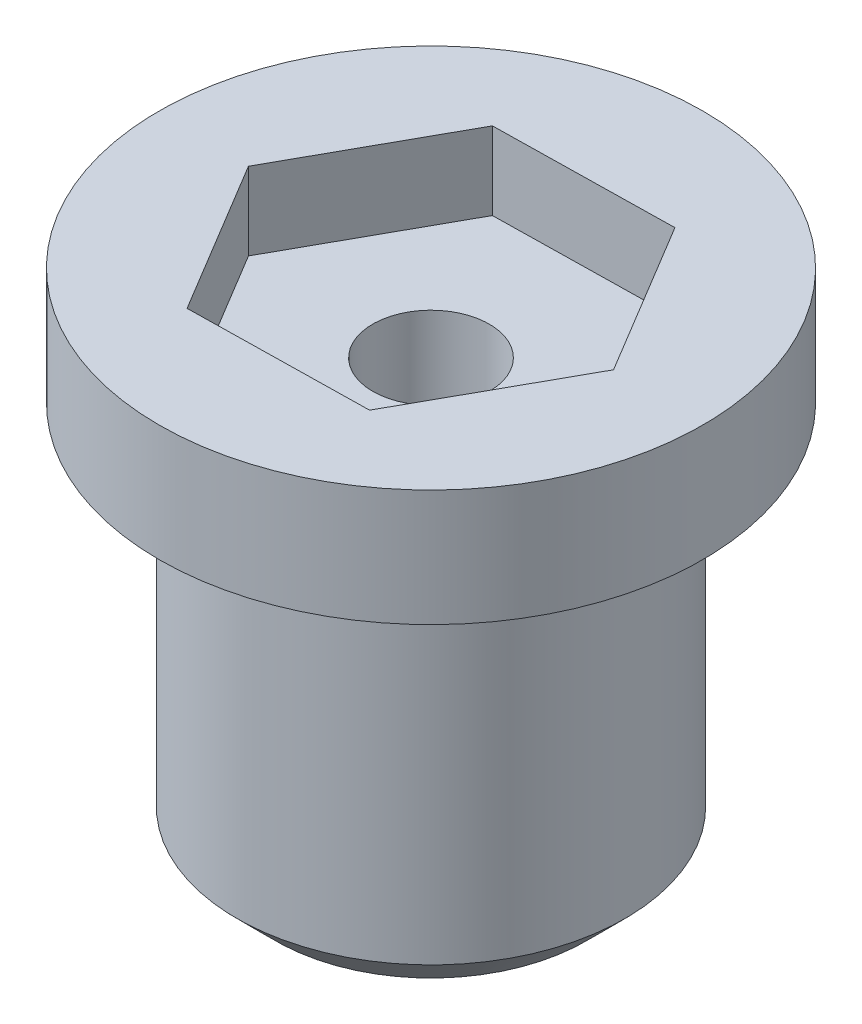
SolidWorks part; units mm, degrees
ref_plane "Front Plane" through (0, 0, 0) normal (0, 0, 1) x (1, 0, 0)
ref_plane "Top Plane" through (0, 0, 0) normal (0, 1, 0) x (1, 0, 0)
ref_plane "Right Plane" through (0, 0, 0) normal (1, 0, 0) x (0, 0, -1)
sketch "Sketch1" plane through (0, 0, 0) normal (0, 0, 1) x (1, 0, 0)
  line L0 (0, 0) -> (4, 0)
  line L1 (4, 0) -> (5, 1)
  line L2 (5, 1) -> (5, 10)
  line L4 (0, 10) -> (0, 0)
  line L5 (5, 10) -> (7, 10)
  line L6 (7, 10) -> (7, 13)
  line L7 (7, 13) -> (0, 13)
  line L8 (0, 13) -> (0, 10)
  line L9 (4, 0) -> (11.6863, 0) construction
  line L10 (0, -4.5707) -> (0, 26.0902) construction
  dimension "D1" = 2
  dimension "D2" = 3
  dimension "D3" = 45
  dimension "D4" = 10
  dimension "D5" = 1.4142
  dimension "D6" = 5
revolve "Revolve1" add sketch "Sketch1" angle 360 about L10
cosmetic thread "Cosmetic Thread1" parameters "D1"=10, "D2"=8.344
sketch "Sketch3" plane through (0, 13, 0) normal (0, 1, 0) x (1, 0, 0)
  circle A0 centre (0, 0) radius 1.5
  dimension "D1" = 3
extrude "Cut-Extrude1" cut sketch "Sketch3" against normal through all
sketch "Sketch4" plane through (0, 13, 0) normal (0, 1, 0) x (1, 0, 0)
  line L1 (2.2395, 4.0395) -> (-2.3786, 3.9593)
  line L2 (-2.3786, 3.9593) -> (-4.6181, -0.0803)
  line L3 (-4.6181, -0.0803) -> (-2.2395, -4.0395)
  line L4 (-2.2395, -4.0395) -> (2.3786, -3.9593)
  line L5 (2.3786, -3.9593) -> (4.6181, 0.0803)
  line L6 (4.6181, 0.0803) -> (2.2395, 4.0395)
  circle A0 centre (0, 0) radius 4 construction
  dimension "D1" = 4
  dimension "D2" = 4.6188
  dimension "D3" = 4.6188
  dimension "D4" = 4.6181
extrude "Cut-Extrude2" cut sketch "Sketch4" against normal blind 2
